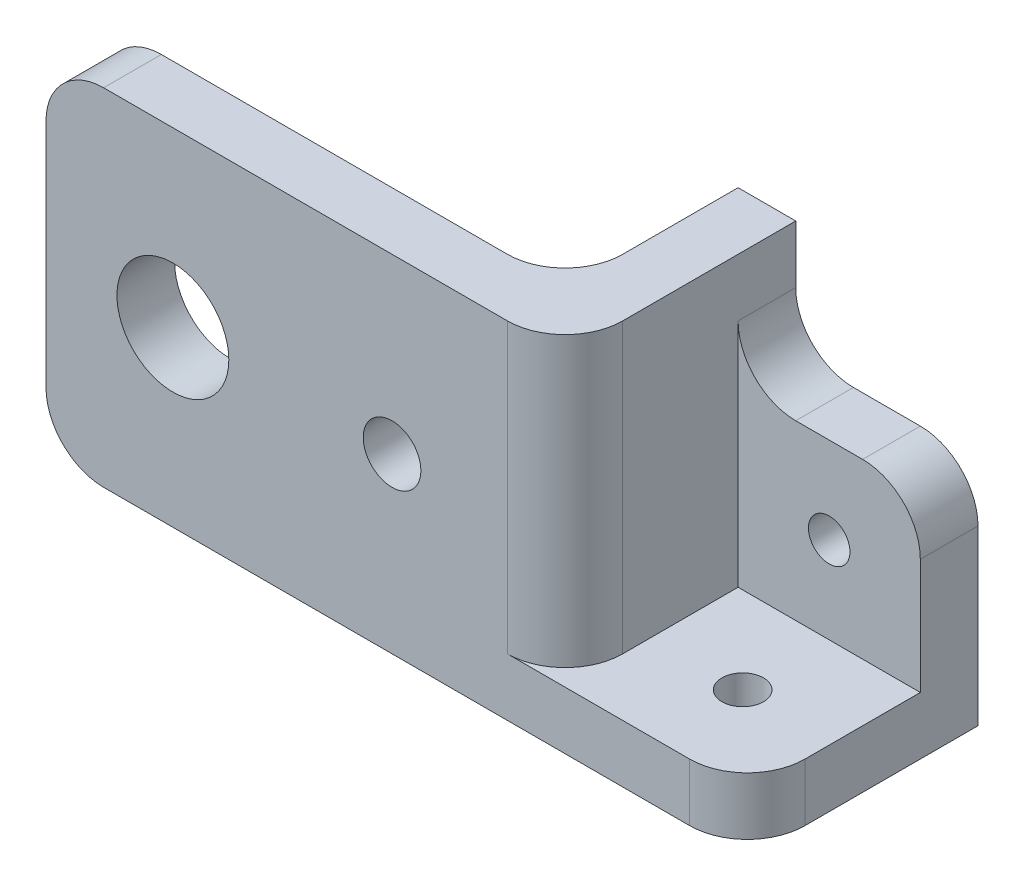
SolidWorks part; units mm, degrees
ref_plane "Front" through (0, 0, 0) normal (0, 0, 1) x (1, 0, 0)
ref_plane "Top" through (0, 0, 0) normal (0, 1, 0) x (1, 0, 0)
ref_plane "Right" through (0, 0, 0) normal (1, 0, 0) x (0, 0, -1)
sketch "Sketch1" plane through (0, 0, 0) normal (0, 1, 0) x (1, 0, 0)
  line L1 (-10.033, -12.7) -> (10.033, -12.7)
  line L2 (-10.033, -12.7) -> (-10.033, 12.7)
  line L3 (-10.033, 12.7) -> (10.033, 12.7)
  line L4 (10.033, -12.7) -> (10.033, 12.7)
  line L5 (-10.033, -12.7) -> (10.033, 12.7) construction
  line L6 (-10.033, 12.7) -> (10.033, -12.7) construction
  point P0 (0, 0)
  dimension "D1" = 20.066
  dimension "D2" = 25.4
extrude "Boss-Extrude1" add sketch "Sketch1" along normal blind 6.35
sketch "Sketch2" plane through (0, 0, -12.7) normal (0, 0, -1) x (-1, 0, 0)
  line L1 (-10.033, 0) -> (10.033, 0)
  line L2 (-10.033, 0) -> (-10.033, 25.4)
  line L3 (-10.033, 25.4) -> (10.033, 25.4)
  line L4 (10.033, 0) -> (10.033, 25.4)
  dimension "D1" = 25.4
extrude "Boss-Extrude2" add sketch "Sketch2" against normal blind 6.35
sketch "Sketch3" plane through (-10.033, 0, 0) normal (-1, 0, 0) x (0, 0, 1)
  line L1 (-12.7, 0) -> (12.7, 0)
  line L2 (-12.7, 0) -> (-12.7, 38.1)
  line L3 (-12.7, 38.1) -> (12.7, 38.1)
  line L4 (12.7, 0) -> (12.7, 38.1)
  dimension "D1" = 38.1
extrude "Boss-Extrude3" add sketch "Sketch3" along normal blind 6.35
sketch "Sketch4" plane through (0, 0, 12.7) normal (0, 0, 1) x (1, 0, 0)
  line L1 (-16.383, 38.1) -> (-67.183, 38.1)
  line L2 (-16.383, 38.1) -> (-16.383, 0)
  line L3 (-16.383, 0) -> (-67.183, 0)
  line L4 (-67.183, 38.1) -> (-67.183, 0)
  dimension "D1" = 50.8
extrude "Boss-Extrude4" add sketch "Sketch4" against normal blind 6.35
sketch "Sketch6" plane through (0, 0, -6.35) normal (0, 0, 1) x (1, 0, 0)
  line L0 (-10.033, 15.875) -> (10.033, 15.875) construction
  line L1 (-10.033, 6.35) -> (-10.033, 25.4) construction
  line L2 (10.033, 25.4) -> (10.033, 6.35) construction
  circle A0 centre (0, 15.875) radius 2.286
  dimension "D1" = 4.572
extrude "Cut-Extrude1" cut sketch "Sketch6" against normal through all
sketch "Sketch7" plane through (0, 6.35, 0) normal (0, 1, 0) x (1, 0, 0)
  line L0 (10.033, -3.175) -> (-10.033, -3.175) construction
  line L1 (10.033, -12.7) -> (10.033, 6.35) construction
  line L2 (-10.033, 6.35) -> (-10.033, -12.7) construction
  circle A0 centre (0, -3.175) radius 2.286
  dimension "D1" = 4.572
extrude "Cut-Extrude2" cut sketch "Sketch7" against normal through all
sketch "Sketch8" plane through (0, 0, 12.7) normal (0, 0, 1) x (1, 0, 0)
  line L0 (-67.183, 19.05) -> (-10.033, 19.05) construction
  line L1 (-67.183, 38.1) -> (-67.183, 0) construction
  line L2 (-10.033, 6.35) -> (-10.033, 38.1) construction
  circle A0 centre (-53.213, 19.05) radius 6.1595
  circle A1 centre (-29.083, 19.05) radius 3.175
  dimension "D1" = 12.319
  dimension "D2" = 13.97
  dimension "D3" = 6.35
  dimension "D4" = 19.05
extrude "Cut-Extrude3" cut sketch "Sketch8" against normal through all
fillet "Fillet1" radius 6.35 7 edges at (-16.383, 19.05, 6.35) (-10.033, 22.225, 12.7) (-10.033, 25.4, -9.525) (10.033, 25.4, -9.525) (10.033, 3.175, 12.7) (-67.183, 0, 9.525) (-67.183, 38.1, 9.525)
